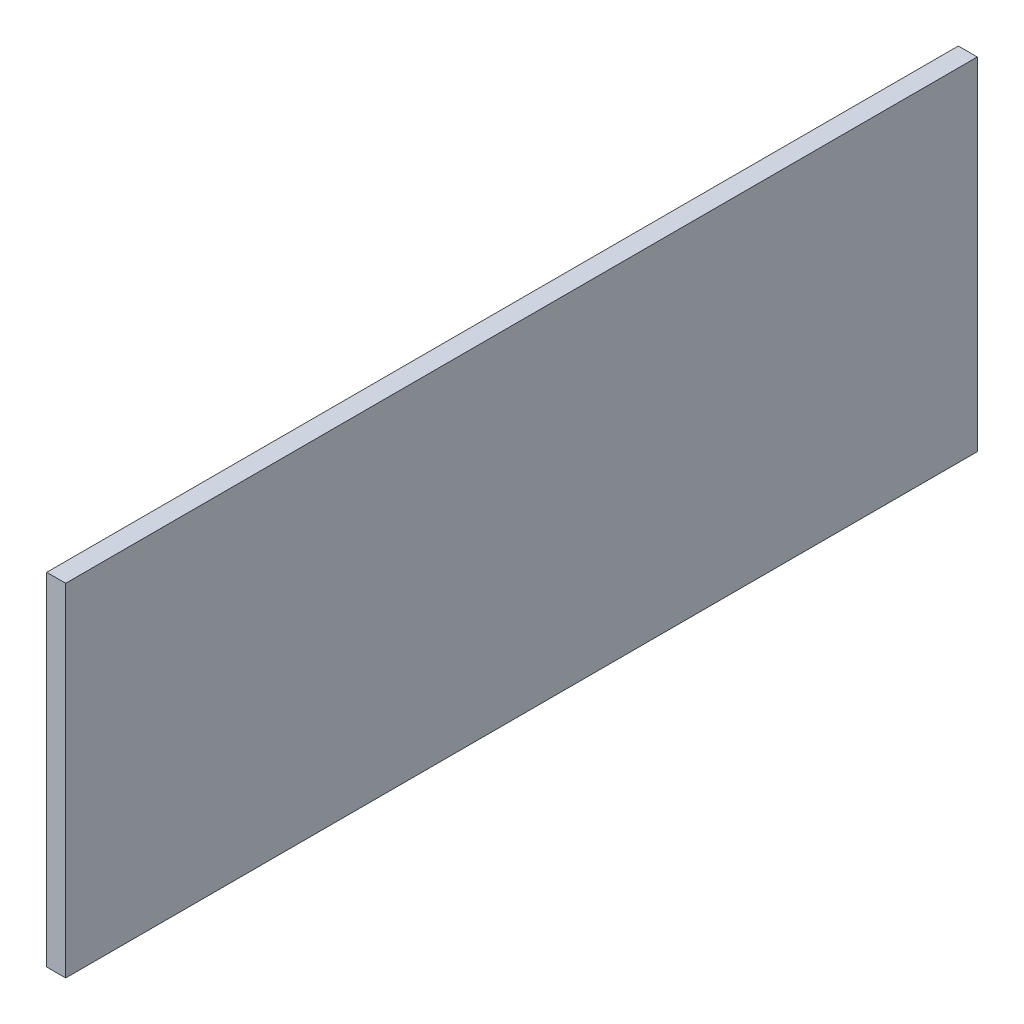
SolidWorks part; units mm, degrees
ref_plane "Front Plane" through (0, 0, 0) normal (0, 0, 1) x (1, 0, 0)
ref_plane "Top Plane" through (0, 0, 0) normal (0, 1, 0) x (1, 0, 0)
ref_plane "Right Plane" through (0, 0, 0) normal (1, 0, 0) x (0, 0, -1)
sketch "Sketch1" plane through (0, 0, 0) normal (1, 0, 0) x (0, 0, -1)
  line L1 (0, 0) -> (-14630.4, 0)
  line L2 (0, 0) -> (0, -5486.4)
  line L3 (0, -5486.4) -> (-14630.4, -5486.4)
  line L4 (-14630.4, 0) -> (-14630.4, -5486.4)
  dimension "D1" = 14630.4
  dimension "D2" = 5486.4
extrude "Boss-Extrude1" add sketch "Sketch1" along normal blind 304.8
